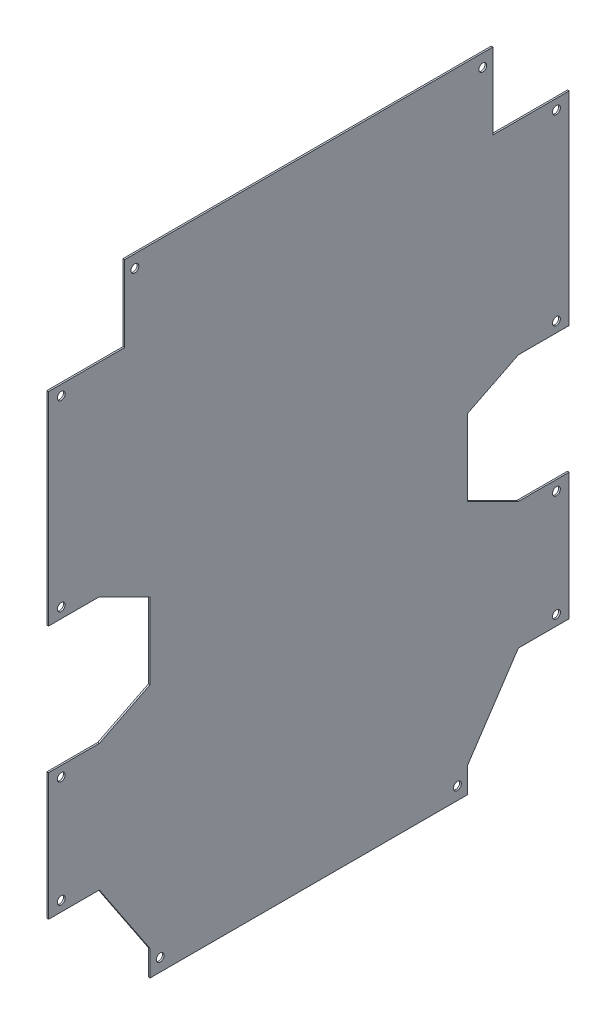
SolidWorks part; units mm, degrees
material "Galvanized Steel"
ref_plane "Front Plane" through (0, 0, 0) normal (0, 0, 1) x (1, 0, 0)
ref_plane "Top Plane" through (0, 0, 0) normal (0, 1, 0) x (1, 0, 0)
ref_plane "Right Plane" through (0, 0, 0) normal (1, 0, 0) x (0, 0, -1)
sketch "Sketch1" plane through (0, 0, 0) normal (1, 0, 0) x (0, 0, -1)
  line L0 (0, 280) -> (40, 280)
  line L1 (0, 0) -> (410, 0)
  line L2 (0, 0) -> (0, 500)
  line L3 (0, 500) -> (410, 500)
  line L4 (410, 0) -> (410, 500)
  line L5 (0, 500) -> (60, 500)
  line L6 (0, 500) -> (0, 440)
  line L7 (0, 440) -> (60, 440)
  line L8 (60, 500) -> (60, 440)
  line L9 (40, 280) -> (80, 260)
  line L10 (80, 260) -> (80, 200)
  line L11 (80, 200) -> (40, 180)
  line L12 (40, 180) -> (0, 180)
  line L13 (0, 80) -> (40, 80)
  line L14 (40, 80) -> (80, 20)
  line L15 (80, 20) -> (80, 0)
  line L16 (205, 500) -> (205, 0) construction
  line L17 (350, 500) -> (350, 440)
  line L18 (410, 440) -> (350, 440)
  line L19 (370, 280) -> (330, 260)
  line L20 (410, 280) -> (370, 280)
  line L21 (330, 260) -> (330, 200)
  line L22 (330, 200) -> (370, 180)
  line L23 (370, 180) -> (410, 180)
  line L24 (410, 80) -> (370, 80)
  line L25 (330, 20) -> (330, 0)
  line L26 (370, 80) -> (330, 20)
  dimension "D1" = 500
  dimension "D2" = 410
  dimension "D3" = 60
  dimension "D4" = 60
  dimension "D5" = 20
  dimension "D6" = 40
  dimension "D7" = 80
  dimension "D8" = 80
  dimension "D9" = 60
  dimension "D10" = 40
  dimension "D11" = 40
  dimension "D12" = 80
  dimension "D13" = 100
  dimension "D14" = 20
  dimension "D15" = 160
extrude "Boss-Extrude1" add sketch "Sketch1" along normal blind 1.3106 contours L3 L16 L1 L25 L26 L24 L4 L23 L22 L21 L19 L20 L18 L17 | L16 L3 L8 L7 L2 L0 L9 L10 L11 L12 L13 L14 L15 L1
sketch "Sketch2" plane through (1.3106, 0, 0) normal (1, 0, 0) x (0, 0, -1)
  line L0 (0, 440) -> (60, 440) construction
  line L1 (60, 500) -> (60, 440) construction
  line L2 (0, 280) -> (40, 280) construction
  line L3 (40, 180) -> (0, 180) construction
  line L4 (0, 80) -> (40, 80) construction
  line L5 (80, 20) -> (80, 0) construction
  line L6 (205, 500) -> (205, 0) construction
  line L7 (60, 500) -> (350, 500) construction
  line L8 (80, 0) -> (330, 0) construction
  circle A1 centre (10, 432) radius 3.1
  circle A3 centre (10, 288) radius 3.1
  circle A4 centre (10, 172) radius 3.1
  circle A5 centre (10, 88) radius 3.1
  circle A6 centre (88, 10) radius 3.1
  circle A7 centre (68, 490) radius 3.1
  circle A8 centre (322, 10) radius 3.1
  circle A9 centre (400, 88) radius 3.1
  circle A10 centre (400, 172) radius 3.1
  circle A11 centre (400, 288) radius 3.1
  circle A12 centre (400, 432) radius 3.1
  circle A13 centre (342, 490) radius 3.1
  dimension "D1" = 6.2
  dimension "D2" = 8
  dimension "D3" = 6.2
  dimension "D5" = 6.2
  dimension "D6" = 8
  dimension "D7" = 6.2
  dimension "D8" = 8
  dimension "D9" = 6.2
  dimension "D10" = 8
  dimension "D11" = 6.2
  dimension "D4" = 8
  dimension "D12" = 8
extrude "Cut-Extrude1" cut sketch "Sketch2" against normal blind 10
